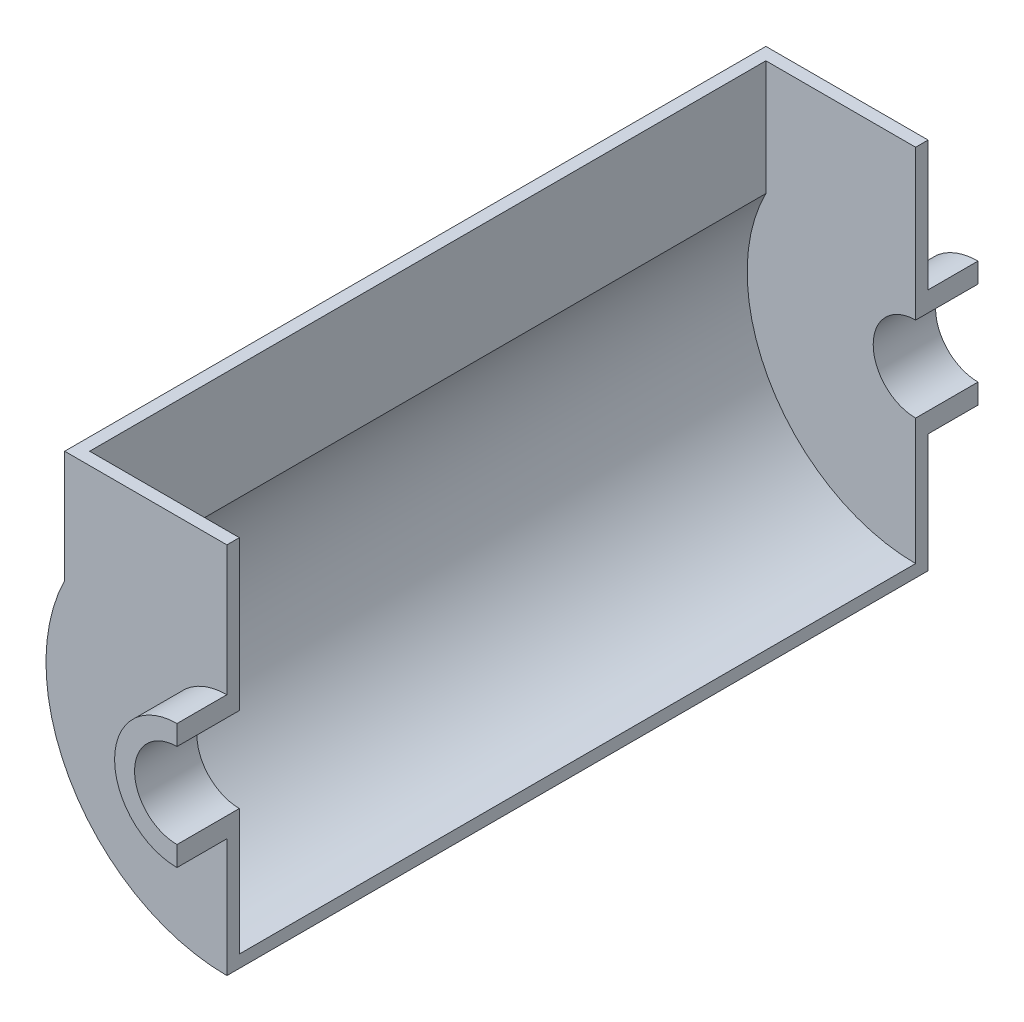
SolidWorks part; units mm, degrees
ref_plane "Front Plane" through (0, 0, 0) normal (0, 0, 1) x (1, 0, 0)
ref_plane "Top Plane" through (0, 0, 0) normal (0, 1, 0) x (1, 0, 0)
ref_plane "Right Plane" through (0, 0, 0) normal (1, 0, 0) x (0, 0, -1)
sketch "Sketch1" plane through (0, 0, 0) normal (0, 0, 1) x (1, 0, 0)
  line L0 (0, 25) -> (0, 17)
  line L1 (0, -17) -> (0, -25)
  arc A0 (0, 25) -> (0, -25) centre (0, 0) ccw
  arc A1 (0, 17) -> (0, -17) centre (0, 0) ccw
  dimension "D1" = 50
  dimension "D2" = 34
extrude "Boss-Extrude1" add sketch "Sketch1" along normal blind 20 and the other way blind 5
sketch "Sketch2" plane through (0, 0, 0) normal (0, 0, 1) x (1, 0, 0)
  line L0 (0, 25) -> (0, 77)
  line L1 (0, 77) -> (-65, 77)
  line L2 (-65, 77) -> (-65, 32.1131)
  line L3 (0, -25) -> (0, -72.5)
  arc A0 (0, 25) -> (0, -25) centre (0, 0) ccw construction
  arc A1 (0, 25) -> (0, -25) centre (0, 0) ccw
  arc A2 (-65, 32.1131) -> (0, -72.5) centre (0, 0) ccw
  point P9 (0, 0)
  dimension "D3" = 72.5
  dimension "D1" = 52
  dimension "D2" = 65
extrude "Boss-Extrude2" add sketch "Sketch2" against normal blind 5
ref_plane "Plane1" through (0, 0, -140.5) normal (0, 0, 1) x (1, 0, 0)
mirror "Mirror12" about plane through (0, 0, -140.5) normal (0, 0, 1) of bodies 102
sketch "Sketch3" plane through (0, 0, -5) normal (0, 0, -1) x (-1, 0, 0)
  line L0 (65, 77) -> (65, 32.1131) construction
  line L1 (65, 77) -> (65, 32.1131)
  line L2 (60, 77) -> (60, 30.9233)
  line L3 (65, 77) -> (60, 77)
  line L4 (0, -72.5) -> (0, -67.5)
  arc A0 (0, -72.5) -> (65, 32.1131) centre (0, 0) ccw construction
  arc A1 (0, -72.5) -> (65, 32.1131) centre (0, 0) ccw
  arc A2 (0, -67.5) -> (60, 30.9233) centre (0, 0) ccw
  dimension "D1" = 5
extrude "Boss-Extrude3" add sketch "Sketch3" along normal up to surface (271 mm away)
